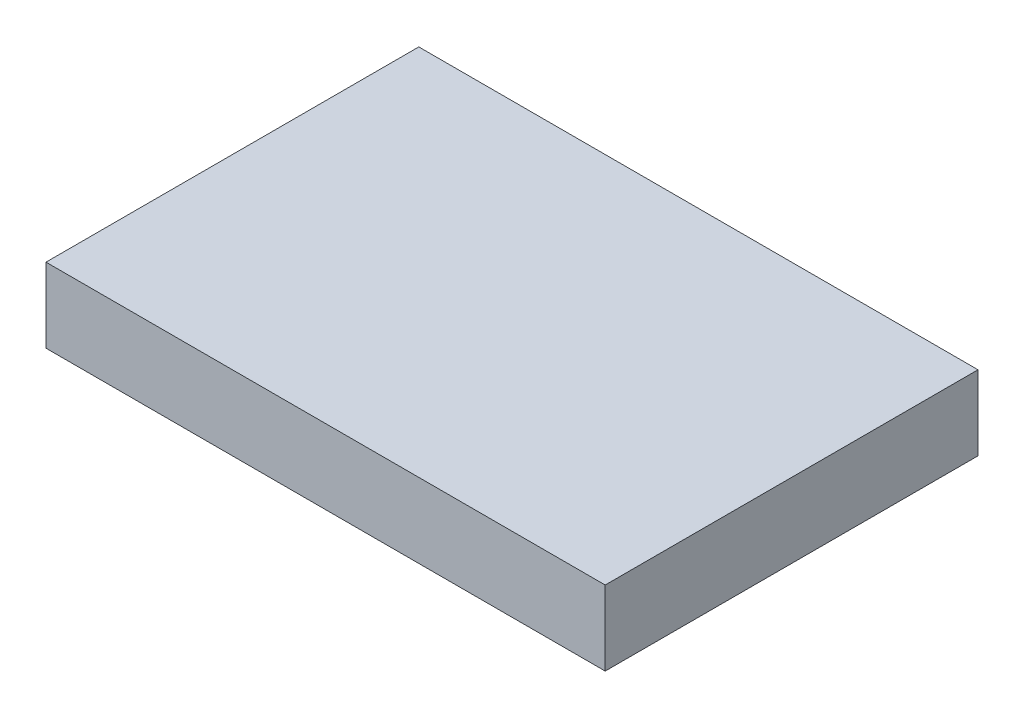
SolidWorks part; units mm, degrees
ref_plane "Front Plane" through (0, 0, 0) normal (0, 0, 1) x (1, 0, 0)
ref_plane "Top Plane" through (0, 0, 0) normal (0, 1, 0) x (1, 0, 0)
ref_plane "Right Plane" through (0, 0, 0) normal (1, 0, 0) x (0, 0, -1)
sketch "Sketch1" plane through (0, 0, 0) normal (0, 1, 0) x (1, 0, 0)
  line L1 (-45720, -30480) -> (45720, -30480)
  line L2 (-45720, -30480) -> (-45720, 30480)
  line L3 (-45720, 30480) -> (45720, 30480)
  line L4 (45720, -30480) -> (45720, 30480)
  line L5 (-45720, -30480) -> (45720, 30480) construction
  line L6 (-45720, 30480) -> (45720, -30480) construction
  point P0 (0, 0)
  dimension "D1" = 91440
  dimension "D2" = 60960
extrude "Boss-Extrude1" add sketch "Sketch1" along normal blind 12192
